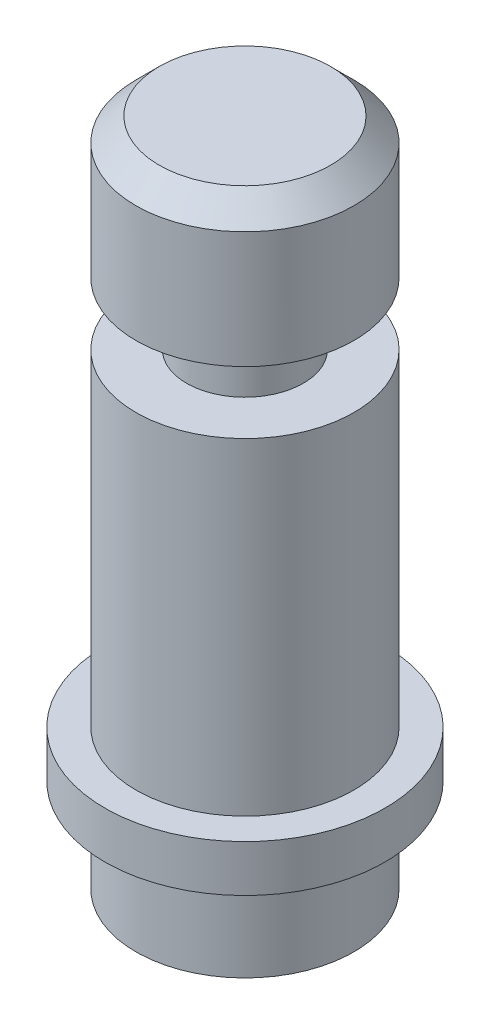
SolidWorks part; units mm, degrees
ref_plane "Front Plane" through (0, 0, 0) normal (0, 0, 1) x (1, 0, 0)
ref_plane "Top Plane" through (0, 0, 0) normal (0, 1, 0) x (1, 0, 0)
ref_plane "Right Plane" through (0, 0, 0) normal (1, 0, 0) x (0, 0, -1)
sketch "Sketch1" plane through (0, 0, 0) normal (0, 0, 1) x (1, 0, 0)
  line L0 (7, 0) -> (0, 0)
  line L1 (0, 0) -> (0, 6)
  line L2 (0, 6) -> (-2, 6)
  line L3 (-2, 6) -> (-2, 9)
  line L4 (-2, 9) -> (0, 9)
  line L5 (0, 9) -> (0, 30)
  line L6 (0, 30) -> (3.25, 30)
  line L7 (3.25, 30) -> (3.25, 34)
  line L8 (3.25, 34) -> (0, 34)
  line L9 (0, 34) -> (0, 43)
  line L10 (0, 43) -> (7, 43)
  line L11 (7, 43) -> (7, 0)
  dimension "D1" = 43
  dimension "D2" = 4
  dimension "D3" = 9
  dimension "D4" = 7
  dimension "D5" = 2
  dimension "D6" = 3
  dimension "D7" = 25
  dimension "D8" = 3.25
revolve "Revolve1" add sketch "Sketch1" angle 360 about L11
chamfer "Chamfer1" distance 1.5 angle 45 1 edges at (0, 43, 0)
